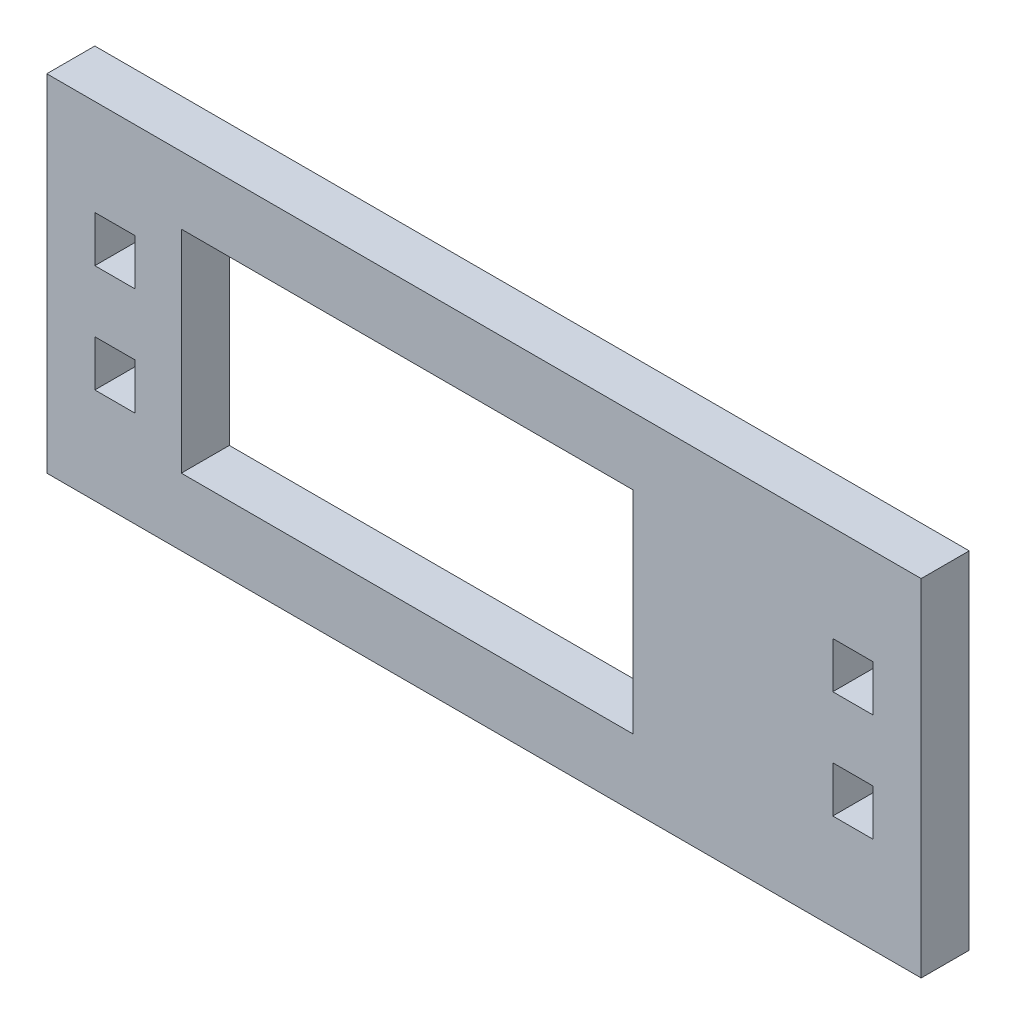
SolidWorks part; units mm, degrees
ref_plane "Front Plane" through (0, 0, 0) normal (0, 0, 1) x (1, 0, 0)
ref_plane "Top Plane" through (0, 0, 0) normal (0, 1, 0) x (1, 0, 0)
ref_plane "Right Plane" through (0, 0, 0) normal (1, 0, 0) x (0, 0, -1)
sketch "Sketch1" plane through (0, 0, 0) normal (0, 0, 1) x (1, 0, 0)
  line L1 (-57.785, -22.86) -> (57.785, -22.86)
  line L2 (-57.785, -22.86) -> (-57.785, 22.86)
  line L3 (-57.785, 22.86) -> (57.785, 22.86)
  line L4 (57.785, -22.86) -> (57.785, 22.86)
  line L5 (-57.785, -22.86) -> (57.785, 22.86) construction
  line L6 (-57.785, 22.86) -> (57.785, -22.86) construction
  point P0 (0, 0)
  dimension "D1" = 115.57
  dimension "D2" = 45.72
extrude "Boss-Extrude1" add sketch "Sketch1" along normal blind 6.35
sketch "Sketch2" plane through (0, 0, 6.35) normal (0, 0, 1) x (1, 0, 0)
  line L1 (-40.005, -13.97) -> (19.685, -13.97)
  line L2 (-40.005, -13.97) -> (-40.005, 13.97)
  line L3 (-40.005, 13.97) -> (19.685, 13.97)
  line L4 (19.685, -13.97) -> (19.685, 13.97)
  line L5 (-40.005, -13.97) -> (19.685, 13.97) construction
  line L6 (-40.005, 13.97) -> (19.685, -13.97) construction
  line L7 (-57.785, 22.86) -> (-57.785, -22.86) construction
  line L9 (57.785, 22.86) -> (-57.785, 22.86) construction
  point P0 (-10.16, 0)
  dimension "D1" = 59.69
  dimension "D2" = 27.94
  dimension "D3" = 17.78
  dimension "D4" = 22.86
extrude "Cut-Extrude1" cut sketch "Sketch2" against normal through all
sketch "Sketch3" plane through (0, 0, 6.35) normal (0, 0, 1) x (1, 0, 0)
  line L0 (-57.785, 22.86) -> (-57.785, -22.86) construction
  line L1 (-51.435, 10.16) -> (-46.101, 10.16)
  line L2 (-51.435, 10.16) -> (-51.435, 4.064)
  line L3 (-51.435, 4.064) -> (-46.101, 4.064)
  line L4 (-46.101, 10.16) -> (-46.101, 4.064)
  line L5 (57.785, 22.86) -> (-57.785, 22.86) construction
  line L6 (-57.785, 0) -> (57.785, 0) construction
  line L7 (57.785, -22.86) -> (57.785, 22.86) construction
  line L8 (0, 22.86) -> (0, -22.86) construction
  line L9 (-57.785, -22.86) -> (57.785, -22.86) construction
  line L10 (-46.101, -10.16) -> (-46.101, -4.064)
  line L11 (-51.435, -4.064) -> (-46.101, -4.064)
  line L12 (-51.435, -10.16) -> (-51.435, -4.064)
  line L13 (-51.435, -10.16) -> (-46.101, -10.16)
  line L14 (51.435, -10.16) -> (46.101, -10.16)
  line L15 (51.435, -10.16) -> (51.435, -4.064)
  line L16 (51.435, -4.064) -> (46.101, -4.064)
  line L17 (46.101, -10.16) -> (46.101, -4.064)
  line L18 (46.101, 10.16) -> (46.101, 4.064)
  line L19 (51.435, 4.064) -> (46.101, 4.064)
  line L20 (51.435, 10.16) -> (51.435, 4.064)
  line L21 (51.435, 10.16) -> (46.101, 10.16)
  dimension "D1" = 6.096
  dimension "D2" = 5.334
  dimension "D3" = 6.35
  dimension "D4" = 12.7
extrude "Cut-Extrude2" cut sketch "Sketch3" against normal through all
